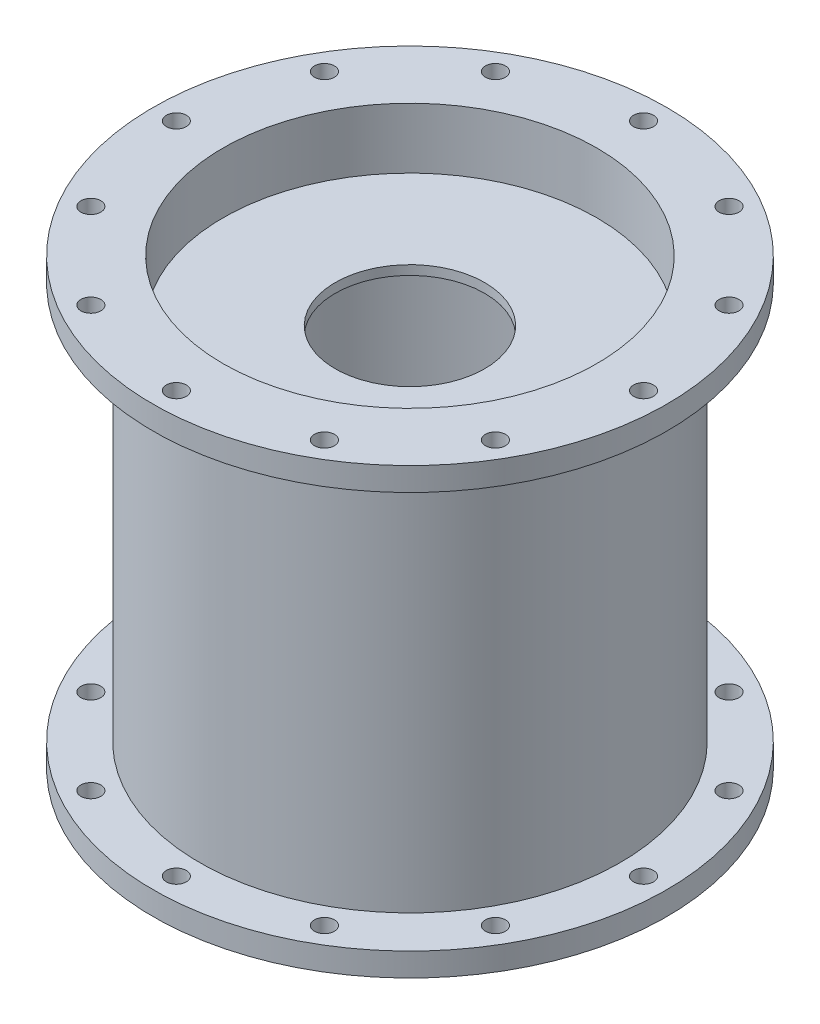
SolidWorks part; units mm, degrees
ref_plane "Front Plane" through (0, 0, 0) normal (0, 0, 1) x (1, 0, 0)
ref_plane "Top Plane" through (0, 0, 0) normal (0, 1, 0) x (1, 0, 0)
ref_plane "Right Plane" through (0, 0, 0) normal (1, 0, 0) x (0, 0, -1)
sketch "Sketch1" plane through (0, 0, 0) normal (1, 0, 0) x (0, 0, -1)
  line L1 (57.15, 6.35) -> (57.15, 114.3)
  line L8 (57.15, 120.65) -> (69.85, 120.65)
  line L9 (69.85, 120.65) -> (69.85, 114.3)
  line L10 (69.85, 114.3) -> (57.15, 114.3)
  line L11 (57.15, 0) -> (69.85, 0)
  line L12 (69.85, 0) -> (69.85, 6.35)
  line L13 (69.85, 6.35) -> (57.15, 6.35)
  line L27 (50.8, 114.3) -> (50.8, 120.65)
  line L28 (50.8, 120.65) -> (57.15, 120.65)
  line L29 (50.8, 6.35) -> (50.8, 0)
  line L30 (50.8, 0) -> (57.15, 0)
  line L31 (50.8, 114.3) -> (50.8, 6.35)
  line L32 (50.8, 0) -> (0, 0) construction
  line L33 (0, 0) -> (0, 6.35) construction
  dimension "D1" = 6.35
  dimension "D2" = 6.35
  dimension "D3" = 12.7
  dimension "D4" = 12.7
  dimension "D5" = 12.7
  dimension "D6" = 12.7
  dimension "D7" = 107.95
  dimension "D8" = 50.8
  dimension "D9" = 6.35
revolve "Chamber" add sketch "Sketch1" angle 360 about L33
sketch "Sketch4" plane through (0, 0, 0) normal (1, 0, 0) x (0, 0, -1)
  line L0 (0, 0) -> (0, 120.65) construction
  line L1 (50.8, 120.65) -> (-50.8, 120.65) construction
  line L3 (50.8, 104.2017) -> (20.32, 104.2017)
  line L7 (50.8, 104.2017) -> (50.8, 101.6617)
  line L8 (0, 60.325) -> (57.15, 60.325) construction
  line L9 (20.32, 104.2017) -> (20.32, 101.6617)
  line L10 (50.8, 16.4483) -> (20.32, 16.4483)
  line L11 (50.8, 16.4483) -> (50.8, 18.9883)
  line L12 (50.8, 18.9883) -> (20.32, 18.9883)
  line L13 (20.32, 16.4483) -> (20.32, 18.9883)
  line L14 (50.8, 101.6617) -> (20.32, 101.6617)
  point P9 (50.7813, 15.9134)
  point P10 (50.342, 18.9883)
  dimension "D2" = 30.48
  dimension "D1" = 2.54
revolve "Turbulence Rings" add sketch "Sketch4" angle 360 about L0
sketch "Sketch5" plane through (0, 120.65, 0) normal (0, 1, 0) x (1, 0, 0)
  line L0 (0, 0) -> (-63.5, 0) construction
  line L1 (0, 0) -> (-54.9926, 31.75) construction
  circle A0 centre (0, 0) radius 63.5 construction
  point P0 (0, 0)
  point P5 (-63.5, 0)
  point P9 (-54.9926, 31.75)
  point P10 (-31.75, 54.9926)
  point P11 (0, 63.5)
  point P12 (31.75, 54.9926)
  point P13 (54.9926, 31.75)
  point P14 (63.5, 0)
  point P15 (54.9926, -31.75)
  point P16 (31.75, -54.9926)
  point P17 (0, -63.5)
  point P18 (-31.75, -54.9926)
  point P19 (-54.9926, -31.75)
  point P20 (0, 0)
  dimension "D3" = 127
  dimension "D1" = 30
  dimension "D2" = 12
hole_wizard "#3 (0.213) Diameter Hole2" positions "Sketch5" profile "Sketch7" hole size "#3" standard "ANSI Inch" end condition through all
sketch "Sketch7" plane through (0, 120.65, 0) normal (1, 0, 0) x (0, 0, 1)
  line L0 (0, 0) -> (0, 120.65)
  line L1 (0, 120.65) -> (2.7051, 120.65)
  line L2 (2.7051, 120.65) -> (2.7051, 0)
  line L5 (2.7051, 0) -> (0, 0)
  line L11 (0, -6.35) -> (0, 107.95) construction
  dimension "Thru Hole Dia." = 5.4102
  dimension "Thru Hole Depth" = 120.65
equation "\"Thickness of Material\"= 0.3in"
equation "\"Chamber Length\"= 4.25in"
equation "\"Flange Length\"= 0.5in"
equation "\"Chamber Wall Thickness\"= 0.25in"
equation "\"Ring Length\"= 1.2in"
equation "\"Ring Thickness\"= 0.1in"
equation "\"Number of Rings\" = 2"
equation "\"Chamber Radius\"= 2in"
equation "\"D1@Sketch4\" = \"Ring Thickness\""
equation "\"D2@Sketch4\"= \"Ring Length\""
equation "\"D7@Sketch1\"= \"Chamber Length\""
equation "\"D9@Sketch1\"= \"Chamber Wall Thickness\""
equation "\"D8@Sketch1\"= \"Chamber Radius\""
equation "\"D4@Sketch1\"= \"Flange Length\""
equation "\"D3@Sketch1\"= \"Flange Length\""
equation "\"Flange Thickness\"= 0.25in"
equation "\"D1@Sketch1\"= \"Flange Thickness\""
equation "\"D5@Sketch1\"= \"Flange Length\""
equation "\"D6@Sketch1\"= \"Flange Length\""
equation "\"D2@Sketch1\"= \"Flange Thickness\""
equation "\"D3@Sketch5\"= 2 * ( \"Chamber Radius\" + \"Chamber Wall Thickness\" + ( \"Flange to Inner Wall Length\" / 2 ) )"
equation "\"Flange to Inner Wall Length\"= ( \"Chamber Radius\" + \"Chamber Wall Thickness\" + \"Flange Length\" ) - ( \"Chamber Radius\" + \"Chamber Wall Thickness\" )"
